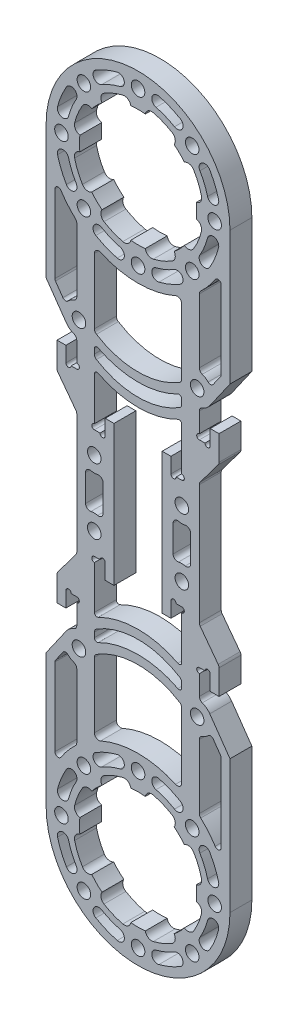
SolidWorks part; units mm, degrees
ref_plane "前视基准面" through (0, 0, 0) normal (0, 0, 1) x (1, 0, 0)
ref_plane "上视基准面" through (0, 0, 0) normal (0, 1, 0) x (1, 0, 0)
ref_plane "右视基准面" through (0, 0, 0) normal (1, 0, 0) x (0, 0, -1)
sketch "草图1" plane through (0, 0, 0) normal (0, 0, 1) x (1, 0, 0)
  line L0 (-5.5, 16.025) -> (-5.5, -16.025)
  line L1 (-5.5, -16.025) -> (-7.5, -16.025)
  line L2 (-7.5, -16.025) -> (-7.5, -12.525)
  line L3 (-7.5, -12.525) -> (-9.975, -12.525)
  line L4 (-9.975, -12.525) -> (-9.975, -49.0203)
  line L5 (0, -67.5) -> (0, 67.5) construction
  line L6 (22.5, 0) -> (-22.5, 0) construction
  line L7 (-14, 51.8475) -> (-14, -51.8475)
  line L8 (5.5, 16.025) -> (5.5, -16.025)
  line L9 (5.5, -16.025) -> (7.5, -16.025)
  line L10 (7.5, -16.025) -> (7.5, -12.525)
  line L11 (7.5, -12.525) -> (9.975, -12.525)
  line L12 (9.975, -12.525) -> (9.975, -49.0203)
  line L13 (14, 51.8475) -> (14, -51.8475)
  line L14 (-9.975, 12.525) -> (-9.975, 49.0203)
  line L15 (-7.5, 12.525) -> (-9.975, 12.525)
  line L16 (-7.5, 16.025) -> (-7.5, 12.525)
  line L17 (-5.5, 16.025) -> (-7.5, 16.025)
  line L18 (7.5, 12.525) -> (9.975, 12.525)
  line L19 (7.5, 16.025) -> (7.5, 12.525)
  line L20 (5.5, 16.025) -> (7.5, 16.025)
  line L21 (9.975, 12.525) -> (9.975, 49.0203)
  circle A0 centre (0, -67.5) radius 13.4
  arc A3 (-14, -51.8475) -> (14, -51.8475) centre (0, -67.5) ccw
  arc A4 (9.975, -49.0203) -> (-9.975, -49.0203) centre (0, -67.5) ccw
  arc A5 (9.975, 49.0203) -> (-9.975, 49.0203) centre (0, 67.5) cw
  circle A6 centre (0, 67.5) radius 13.4
  arc A7 (-14, 51.8475) -> (14, 51.8475) centre (0, 67.5) cw
  point P10 (0, 0)
  point P16 (0, 0)
  point P26 (-14, 0)
  point P31 (-5.5, 0)
  point P35 (5.5, 0)
  point P36 (14, 0)
  dimension "D2" = 42
  dimension "D3" = 26.8
  dimension "D1" = 135
  dimension "D4" = 11
  dimension "D5" = 2
  dimension "D6" = 3.5
  dimension "D7" = 45
  dimension "D8" = 25.05
  dimension "D9" = 19.95
  dimension "D10" = 28
extrude "凸台-拉伸1" add sketch "草图1" along normal mid plane 5
sketch "草图2" plane through (0, 0, -2.5) normal (0, 0, -1) x (-1, 0, 0)
  line L0 (-7.5, 12.525) -> (-9.975, 12.525) construction
  line L1 (-9.975, 12.525) -> (-9.975, 49.0203) construction
  line L2 (-9.975, -49.0203) -> (-9.975, -12.525) construction
  line L3 (-9.975, -12.525) -> (-7.5, -12.525) construction
  circle A0 centre (-8.1, 12.525) radius 0.6
  circle A1 centre (-9.975, 13.125) radius 0.6
  circle A2 centre (-9.975, -13.125) radius 0.6
  circle A3 centre (-8.1, -12.525) radius 0.6
  dimension "D1" = 1.2
extrude "切除-拉伸1" cut sketch "草图2" against normal through all
mirror "镜向1" about plane through (0, 0, 0) normal (1, 0, 0) of "切除-拉伸1"
sketch "草图3" plane through (0, 0, -2.5) normal (0, 0, -1) x (-1, 0, 0)
  circle A0 centre (0, 67.5) radius 17.5 construction
  circle A1 centre (0, 85) radius 1.55
  circle A2 centre (12.3744, 79.8744) radius 1.55
  circle A3 centre (17.5, 67.5) radius 1.55
  circle A4 centre (12.3744, 55.1256) radius 1.55
  circle A5 centre (0, 50) radius 1.55
  circle A6 centre (-12.3744, 55.1256) radius 1.55
  circle A7 centre (-17.5, 67.5) radius 1.55
  circle A8 centre (-12.3744, 79.8744) radius 1.55
  point P21 (0, 67.5)
  dimension "D1" = 3.1
  dimension "D2" = 35
  dimension "D3" = 8
extrude "切除-拉伸2" cut sketch "草图3" against normal through all
mirror "镜向2" about plane through (0, 0, 0) normal (0, 1, 0) of "切除-拉伸2"
sketch "草图4" plane through (0, 0, -2.5) normal (0, 0, -1) x (-1, 0, 0)
  line L0 (-5.5, 0) -> (-14, 0) construction
  line L1 (-5.5, -16.025) -> (-5.5, 16.025) construction
  line L2 (-14, -51.8475) -> (-14, 51.8475) construction
  line L3 (0, -16.025) -> (0, 16.025) construction
  line L4 (-5.5, 16.025) -> (-7.5, 16.025) construction
  line L5 (-12, 4.567) -> (-12, -4.567)
  line L6 (-8, 4.567) -> (-8, -4.567)
  line L7 (8, 4.567) -> (8, -4.567)
  line L8 (12, 4.567) -> (12, -4.567)
  line L10 (13.5, -32.5) -> (-13.5, -32.5) construction
  line L11 (13.5, -32.5) -> (13.5, 32.5) construction
  line L12 (13.5, 32.5) -> (-13.5, 32.5) construction
  line L13 (-13.5, -32.5) -> (-13.5, 32.5) construction
  line L14 (13.5, -32.5) -> (-13.5, 32.5) construction
  line L15 (13.5, 32.5) -> (-13.5, -32.5) construction
  circle A0 centre (-10, 7.5) radius 1.55
  circle A2 centre (-10, -7.5) radius 1.55
  circle A3 centre (10, -7.5) radius 1.55
  circle A4 centre (10, 7.5) radius 1.55
  arc A5 (-12, 4.567) -> (-8, 4.567) centre (-10, 7.5) ccw
  arc A6 (-8, -4.567) -> (-12, -4.567) centre (-10, -7.5) ccw
  arc A7 (12, 4.567) -> (8, 4.567) centre (10, 7.5) cw
  arc A8 (8, -4.567) -> (12, -4.567) centre (10, -7.5) cw
  circle A9 centre (-13.5, 32.5) radius 1.55
  circle A10 centre (13.5, 32.5) radius 1.55
  circle A11 centre (-13.5, -32.5) radius 1.55
  circle A12 centre (13.5, -32.5) radius 1.55
  circle A13 centre (-13.5, 32.5) radius 3.5 construction
  circle A14 centre (0, 67.5) radius 13.4 construction
  point P12 (0, 0)
  point P29 (0, 0)
  dimension "D1" = 15
  dimension "D2" = 10
  dimension "D3" = 3.1
  dimension "D4" = 2
  dimension "D5" = 2
  dimension "D6" = 7
  dimension "D7" = 35
  dimension "D8" = 27
extrude "切除-拉伸3" cut sketch "草图4" against normal through all
fillet "圆角1" radius 1 8 edges at (-12, -4.567, 0) (-8, 4.567, 0) (-12, 4.567, 0) (-8, -4.567, 0) (12, -4.567, 0) (8, -4.567, 0) (8, 4.567, 0) (12, 4.567, 0)
sketch "草图5" plane through (0, 0, -2.5) normal (0, 0, -1) x (-1, 0, 0)
  line L0 (-9.975, 13.725) -> (-9.975, 49.0203) construction
  circle A0 centre (-13.5, 32.5) radius 3.525
  circle A1 centre (-13.5, 32.5) radius 1.55
  circle A2 centre (13.5, 32.5) radius 1.55
  circle A4 centre (13.5, 32.5) radius 3.525
  circle A5 centre (-13.5, -32.5) radius 1.55
  circle A6 centre (13.5, -32.5) radius 1.55
  circle A7 centre (13.5, -32.5) radius 3.525
  circle A8 centre (-13.5, -32.5) radius 3.525
extrude "凸台-拉伸2" add sketch "草图5" against normal blind 5
fillet "圆角2" radius 1 16 edges at (9.975, -49.0203, 0) (-9.975, -49.0203, 0) (9.975, 49.0203, 0) (-9.975, 49.0203, 0) (14, -29.0106, 0) (14, -35.9894, 0) (14, -51.8475, 0) (-14, -51.8475, 0) (-14, -29.0106, 0) (-14, -35.9894, 0) (-14, 29.0106, 0) (-14, 35.9894, 0) (14, 51.8475, 0) (14, 35.9894, 0) (14, 29.0106, 0) (-14, 51.8475, 0)
sketch "草图6" plane through (0, 0, 2.5) normal (0, 0, 1) x (1, 0, 0)
  line L0 (-7.0015, 78.9254) -> (0, 67.5) construction
  line L1 (0, 67.5) -> (-3.1282, 80.5298) construction
  line L2 (-12.3744, 79.8744) -> (0, 85) construction
  line L4 (-7.0015, 78.9254) -> (-3.1282, 80.5298) construction
  arc A0 (-7.7852, 80.2043) -> (-8.2346, 78.0713) centre (-7.0015, 78.9254) ccw
  arc A1 (-1.6523, 80.7977) -> (-3.4783, 81.9883) centre (-3.1282, 80.5298) ccw
  circle A2 centre (0, 67.5) radius 13.4 construction
  arc A3 (-3.4783, 81.9883) -> (-7.7852, 80.2043) centre (0, 67.5) ccw
  arc A4 (-1.6523, 80.7977) -> (-8.2346, 78.0713) centre (0, 67.5) ccw
  dimension "D1" = 18
  dimension "D2" = 3
extrude "切除-拉伸4" cut sketch "草图6" against normal through all
pattern_circular "阵列(圆周)1" count 8 over 360 about axis through (0, 67.5, 0) along (0, 0, 1) of "切除-拉伸4"
mirror "镜向3" about plane through (0, 0, 0) normal (0, 1, 0) of "阵列(圆周)1", "切除-拉伸4"
sketch "草图7" plane through (0, 0, 2.5) normal (0, 0, 1) x (1, 0, 0)
  line L0 (-17.5, 67.5) -> (-12.3744, 55.1256) construction
  line L1 (-17.1362, 63.0683) -> (-15.2508, 58.5166) construction
  line L2 (-17.1362, 63.0683) -> (0, 67.5) construction
  line L3 (0, 67.5) -> (-15.2508, 58.5166) construction
  arc A0 (-15.2508, 58.5166) -> (-17.1362, 63.0683) centre (0, 67.5) cw construction
  arc A1 (-18.3948, 62.7428) -> (-16.371, 57.8568) centre (0, 67.5) ccw
  arc A2 (-15.8776, 63.3938) -> (-14.1307, 59.1764) centre (0, 67.5) ccw
  arc A3 (-15.8776, 63.3938) -> (-18.3948, 62.7428) centre (-17.1362, 63.0683) ccw
  arc A4 (-16.371, 57.8568) -> (-14.1307, 59.1764) centre (-15.2508, 58.5166) ccw
  arc A5 (14.3182, 52.138) -> (-14.3182, 52.138) centre (0, 67.5) ccw construction
  arc A6 (-14.4883, 64.0217) -> (-12.7043, 59.7148) centre (0, 67.5) ccw construction
  point P4 (-16.3527, 60.7265)
  dimension "D1" = 2
  dimension "D2" = 1.5
  dimension "D3" = 16
extrude "切除-拉伸5" cut sketch "草图7" against normal through all
pattern_circular "阵列(圆周)2" count 8 over 360 about axis through (0, 67.5, 0) along (0, 0, 1) of "切除-拉伸5"
mirror "镜向4" about plane through (0, 0, 0) normal (0, 1, 0) of "阵列(圆周)2", "切除-拉伸5"
sketch "草图8" plane through (0, 0, 2.5) normal (0, 0, 1) x (1, 0, 0)
  line L0 (-14, -22.525) -> (-16.48, -22.525)
  line L1 (-14, 28.2309) -> (-14, -28.2309) construction
  line L2 (-16.48, -22.525) -> (-16.48, -26)
  line L3 (-16.48, -26) -> (-18.5, -26)
  line L4 (-18.5, -26) -> (-18.5, -20)
  line L5 (-14, 0) -> (14, 0) construction
  line L6 (14, -28.2309) -> (14, 28.2309) construction
  line L7 (-14, 22.525) -> (-16.48, 22.525)
  line L8 (-16.48, 22.525) -> (-16.48, 26)
  line L9 (-16.48, 26) -> (-18.5, 26)
  line L10 (-18.5, 0) -> (-14, 0) construction
  line L11 (-14, 22.525) -> (-14, 14)
  line L12 (-18.5, -20) -> (-14, -14)
  line L13 (-18.5, 20) -> (-18.5, 26)
  line L14 (-14, -14) -> (-14, -22.525)
  line L15 (-18.5, 20) -> (-14, 14)
  dimension "D1" = 45.05
  dimension "D2" = 2.48
  dimension "D3" = 4.5
  dimension "D4" = 52
  dimension "D5" = 28
  dimension "D6" = 40
extrude "凸台-拉伸3" add sketch "草图8" against normal up to surface (5 mm away)
mirror "镜向6" about plane through (0, 0, 0) normal (1, 0, 0) of "凸台-拉伸3"
sketch "草图10" plane through (0, 0, 2.5) normal (0, 0, 1) x (1, 0, 0)
  line L0 (-14, 22.525) -> (-16.48, 22.525) construction
  line L1 (-14, 28.2309) -> (-14, 22.525) construction
  line L2 (-16.48, -22.525) -> (-14, -22.525) construction
  line L3 (-14, -22.525) -> (-14, -28.2309) construction
  circle A0 centre (-15.88, 22.525) radius 0.6
  circle A1 centre (-14, 23.125) radius 0.6
  circle A2 centre (-15.88, -22.525) radius 0.6
  circle A3 centre (-14, -23.125) radius 0.6
  dimension "D1" = 1.2
extrude "切除-拉伸6" cut sketch "草图10" against normal through all
fillet "圆角3" radius 1 8 edges at (-18.5, 20, 0) (-14, 14, 0) (-14, -14, 0) (-18.5, -20, 0) (14, 14, 0) (18.5, 20, 0) (14, -14, 0) (18.5, -20, 0)
sketch "草图11" plane through (0, 0, 2.5) normal (0, 0, 1) x (1, 0, 0)
  line L0 (-16.9792, -33.0666) -> (-20, -37.3808) construction
  line L1 (-20, -37.3808) -> (-20, -61.0969) construction
  line L2 (-16.3875, -30.4781) -> (-21, -37.0655)
  line L3 (-21, -37.0655) -> (-21, -67.5)
  line L5 (-19, -37.6961) -> (-19, -58.5557)
  line L6 (-21, -37.0655) -> (-21, -61.0969) construction
  line L7 (-19, -37.6961) -> (-19, -61.0969) construction
  line L8 (-16.3875, -30.4781) -> (-21, -37.0655) construction
  line L9 (-14.7492, -31.6253) -> (-19, -37.6961) construction
  line L10 (14, -14) -> (14, 14) construction
  line L11 (-14, -36.7691) -> (-14, -51.4065) construction
  line L13 (-16.5721, -34.2286) -> (-19, -37.6961)
  line L14 (-14, 0) -> (14, 0) construction
  line L15 (-14, 13.6667) -> (-14, -13.6667) construction
  line L22 (-15.5684, -31.0517) -> (-20, -37.3808) construction
  line L23 (-16.3875, 30.4781) -> (-21, 37.0655)
  line L24 (-21, 37.0655) -> (-21, 67.5)
  line L25 (-19, 37.6961) -> (-19, 58.5557)
  line L26 (-16.5721, 34.2286) -> (-19, 37.6961)
  arc A0 (-14.3182, -52.138) -> (14.3182, -52.138) centre (0, -67.5) ccw construction
  arc A1 (-19, -58.5557) -> (-21, -67.5) centre (0, -67.5) ccw
  arc A2 (-14.6685, -29.1743) -> (-14.6685, -35.8257) centre (-13.5, -32.5) ccw construction
  arc A3 (-16.3875, -30.4781) -> (-16.5721, -34.2286) centre (-13.5, -32.5) ccw
  arc A11 (-19, 58.5557) -> (-21, 67.5) centre (0, 67.5) cw
  arc A12 (-16.3875, 30.4781) -> (-16.5721, 34.2286) centre (-13.5, 32.5) cw
  point P2 (14, 0)
  point P28 (0, 0)
  point P30 (-14, 0)
  point P31 (0, 0)
  point P36 (0, 0)
  point P46 (-16.9982, -32.934)
  dimension "D4" = 35
  dimension "D1" = 1
  dimension "D2" = 1
extrude "凸台-拉伸4" add sketch "草图11" against normal blind 5
mirror "镜向5" about plane through (0, 0, 0) normal (1, 0, 0) of "凸台-拉伸4"
fillet "圆角4" radius 0.75 12 edges at (-19, -37.6961, 0) (-19, -58.5557, 0) (-16.5721, -34.2286, 0) (19, -37.6961, 0) (19, -58.5557, 0) (16.5721, -34.2286, 0) (19, 37.6961, 0) (19, 58.5557, 0) (16.5721, 34.2286, 0) (-19, 37.6961, 0) (-19, 58.5557, 0) (-16.5721, 34.2286, 0)
mirror "镜向7" about plane through (0, 0, 0) normal (1, 0, 0) of "切除-拉伸6"
sketch "草图12" plane through (0, 0, -2.5) normal (0, 0, -1) x (-1, 0, 0)
  line L0 (-16.3875, -30.4781) -> (-21, -37.0655) construction
  line L1 (16.3875, -30.4781) -> (21, -37.0655) construction
  line L2 (9.975, -13.725) -> (9.975, -47.414) construction
  line L3 (-9.975, -47.414) -> (-9.975, -13.725) construction
  line L4 (9.975, -24.6084) -> (9.975, -26.96)
  line L5 (-9.975, -26.96) -> (-9.975, -24.6084)
  arc A0 (9.975, -24.6084) -> (-9.975, -24.6084) centre (0, -41.9433) ccw
  arc A1 (9.975, -26.96) -> (-9.975, -26.96) centre (0, -41.9433) ccw
  circle A2 centre (0, -41.9433) radius 18 construction
  circle A3 centre (0, -41.9433) radius 20 construction
  point P6 (0, -43.1728)
  dimension "D1" = 40
  dimension "D2" = 2
extrude "凸台-拉伸5" add sketch "草图12" against normal blind 5
pattern_linear "阵列(线性)1" count 2 spacing 5 along (0, -1, 0) of "凸台-拉伸5"
mirror "镜向8" about plane through (0, 0, 0) normal (0, 1, 0) of "阵列(线性)1", "凸台-拉伸5"
fillet "圆角5" radius 0.6 8 edges at (-9.975, 24.6084, 0) (9.975, 24.6084, 0) (9.975, -24.6084, 0) (-9.975, -24.6084, 0) (-9.975, 29.6084, 0) (9.975, 29.6084, 0) (9.975, -29.6084, 0) (-9.975, -29.6084, 0)
fillet "圆角6" radius 1 8 edges at (-9.975, 31.96, 0) (-9.975, 26.96, 0) (9.975, 31.96, 0) (9.975, 26.96, 0) (-9.975, -26.96, 0) (-9.975, -31.96, 0) (9.975, -31.96, 0) (9.975, -26.96, 0)
